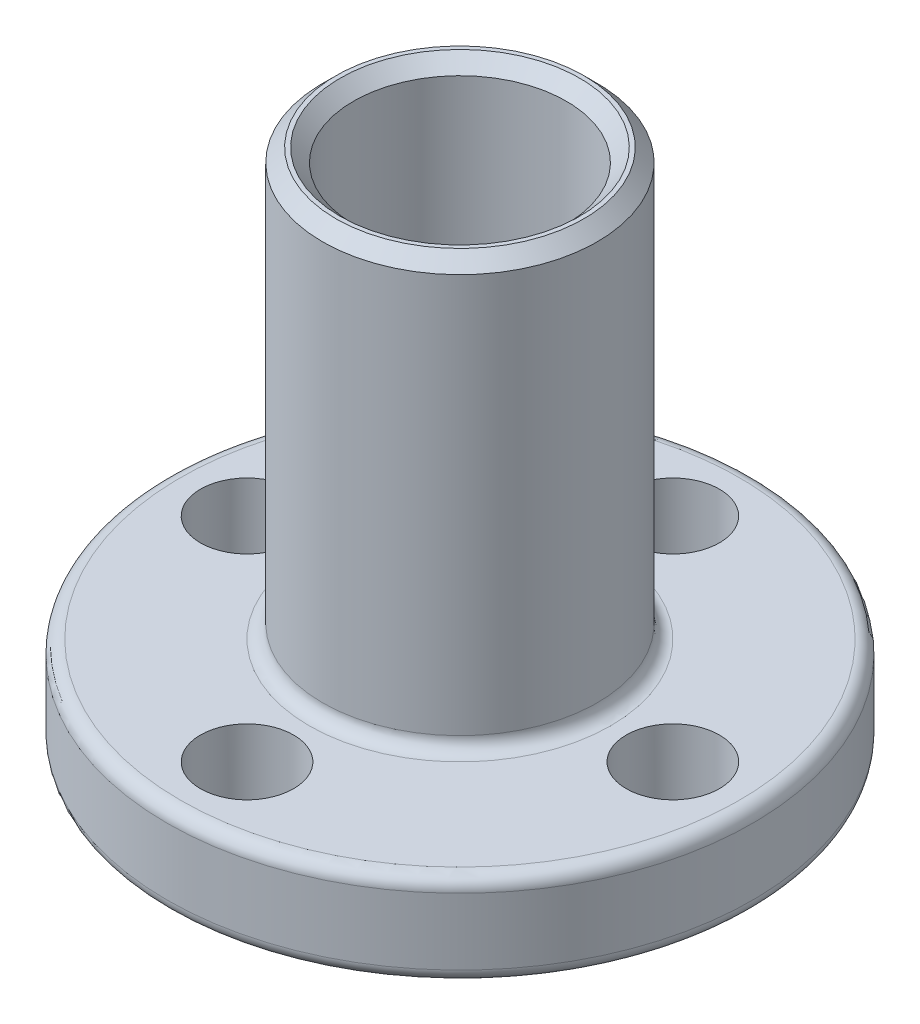
SolidWorks part; units mm, degrees
material "1023 Carbon Steel Sheet (SS)"
ref_plane "Front Plane" through (0, 0, 0) normal (0, 0, 1) x (1, 0, 0)
ref_plane "Top Plane" through (0, 0, 0) normal (0, 1, 0) x (1, 0, 0)
ref_plane "Right Plane" through (0, 0, 0) normal (1, 0, 0) x (0, 0, -1)
sketch "Sketch1" plane through (0, 0, 0) normal (0, 1, 0) x (1, 0, 0)
  circle A0 centre (0, 0) radius 5.16
  dimension "D1" = 10.32
extrude "Boss-Extrude1" add sketch "Sketch1" along normal blind 1.5
sketch "Sketch2" plane through (0, 1.5, 0) normal (0, 1, 0) x (1, 0, 0)
  circle A0 centre (0, 0) radius 11
  dimension "D1" = 22
extrude "Boss-Extrude2" add sketch "Sketch2" along normal blind 3.5
sketch "Sketch3" plane through (0, 5, 0) normal (0, 1, 0) x (1, 0, 0)
  circle A0 centre (0, 0) radius 5.16
  dimension "D1" = 10.32
extrude "Boss-Extrude3" add sketch "Sketch3" along normal blind 16
sketch "Sketch4" plane through (0, 21, 0) normal (0, 1, 0) x (1, 0, 0)
  circle A0 centre (0, 0) radius 4
  dimension "D1" = 8
extrude "Cut-Extrude1" cut sketch "Sketch4" against normal blind 26
sketch "Sketch5" plane through (0, 5, 0) normal (0, 1, 0) x (1, 0, 0)
  line L0 (0, 0) -> (0, 11) construction
  circle A0 centre (0, 0) radius 11 construction
  circle A1 centre (0, 8) radius 1.75
  dimension "D1" = 3.5
  dimension "D2" = 8
extrude "Cut-Extrude2" cut sketch "Sketch5" against normal blind 26
pattern_circular "CirPattern1" count 4 over 360 about axis through (0, 0, 0) along (0, 1, 0) of "Cut-Extrude2"
fillet "Fillet1" radius 0.5 4 edges at (0, 1.5, 5.16) (0, 5, 11) (0, 1.5, 11) (0, 5, 5.16)
chamfer "Chamfer1" distance 0.5 angle 45 4 edges at (0, 0, 5.16) (0, 21, 5.16) (0, 21, 4) (0, 0, 4)
